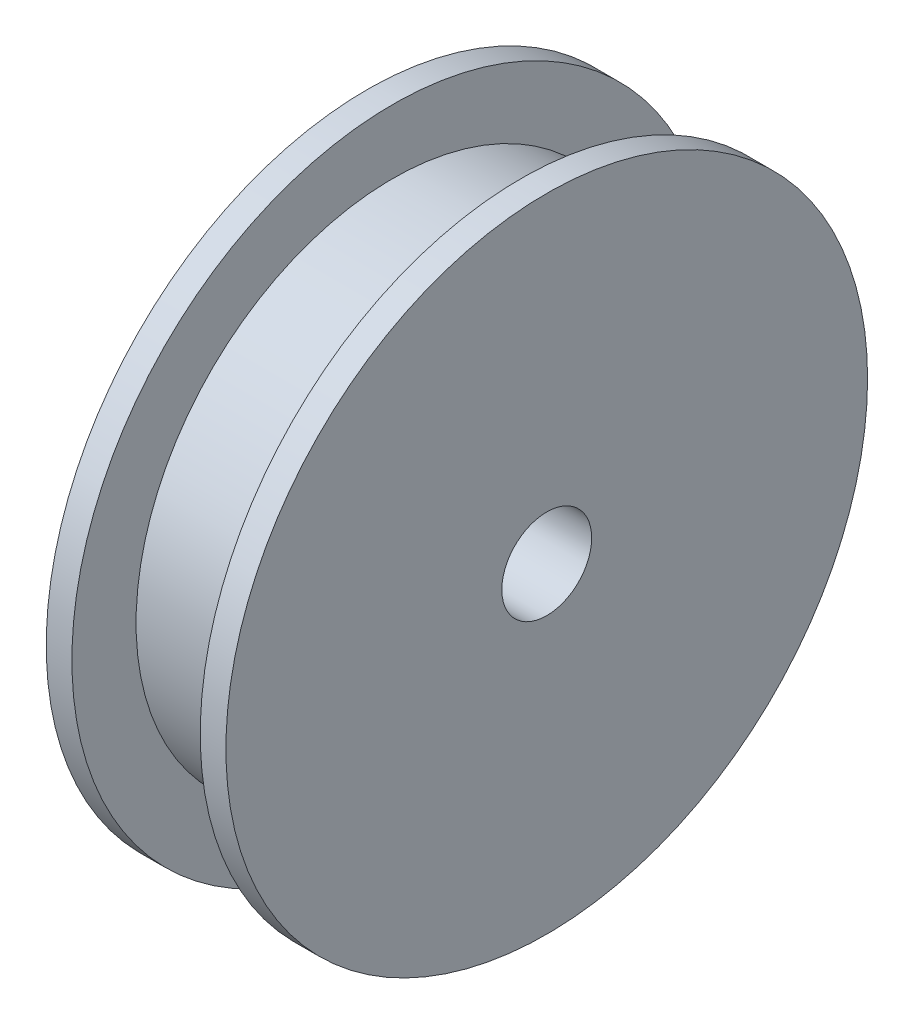
SolidWorks part; units mm, degrees
ref_plane "Front Plane" through (0, 0, 0) normal (0, 0, 1) x (1, 0, 0)
ref_plane "Top Plane" through (0, 0, 0) normal (0, 1, 0) x (1, 0, 0)
ref_plane "Right Plane" through (0, 0, 0) normal (1, 0, 0) x (0, 0, -1)
sketch "Sketch1" plane through (0, 0, 0) normal (1, 0, 0) x (0, 0, -1)
  circle A0 centre (0, 0) radius 25
  dimension "D1" = 50
extrude "Boss-Extrude1" add sketch "Sketch1" along normal blind 2
sketch "Sketch2" plane through (2, 0, 0) normal (1, 0, 0) x (0, 0, -1)
  circle A0 centre (0, 0) radius 20
  dimension "D1" = 40
extrude "Boss-Extrude2" add sketch "Sketch2" along normal blind 10
sketch "Sketch3" plane through (12, 0, 0) normal (1, 0, 0) x (0, 0, -1)
  circle A0 centre (0, 0) radius 25
  dimension "D1" = 50
extrude "Boss-Extrude3" add sketch "Sketch3" along normal blind 2
sketch "Sketch4" plane through (0, 0, 0) normal (-1, 0, 0) x (0, 0, 1)
  circle A0 centre (0, 0) radius 3.5
  dimension "D1" = 7
extrude "Cut-Extrude1" cut sketch "Sketch4" against normal blind 19
